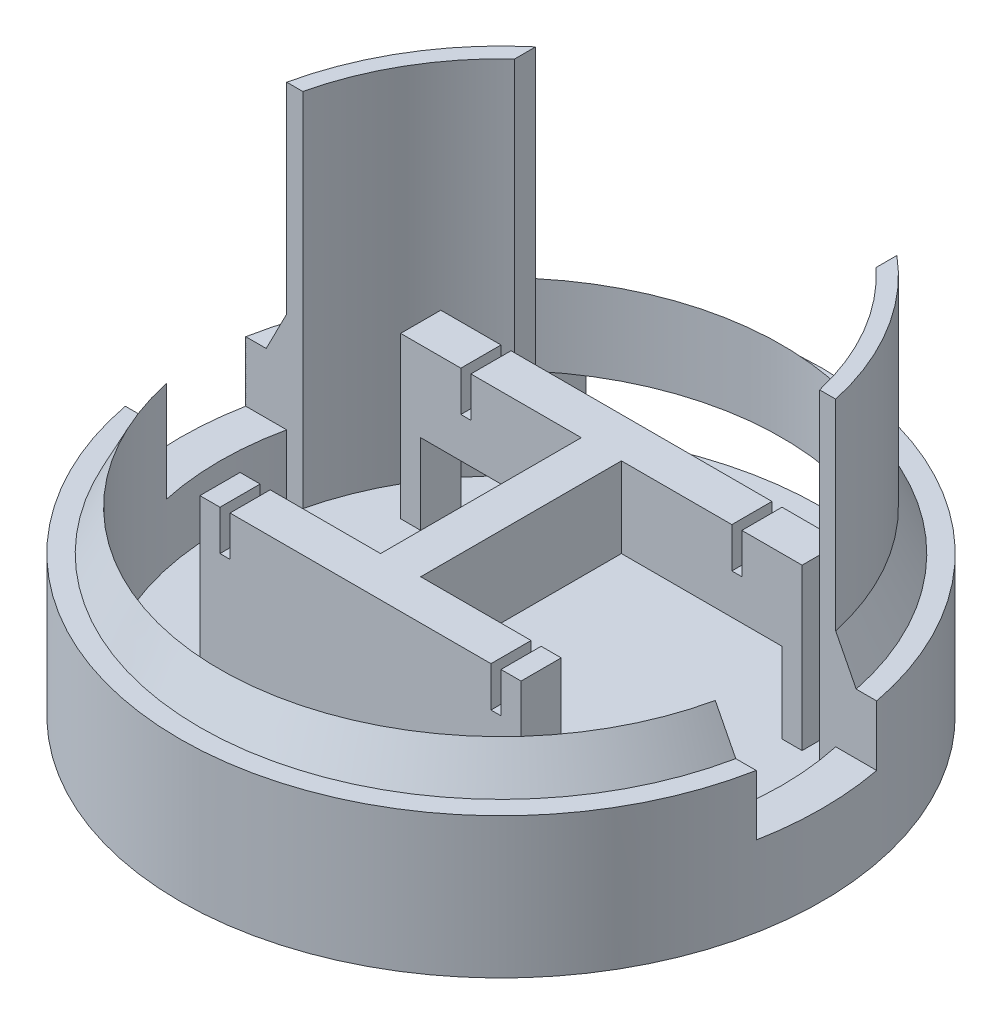
SolidWorks part; units mm, degrees
ref_plane "Front Plane" through (0, 0, 0) normal (0, 0, 1) x (1, 0, 0)
ref_plane "Top Plane" through (0, 0, 0) normal (0, 1, 0) x (1, 0, 0)
ref_plane "Right Plane" through (0, 0, 0) normal (1, 0, 0) x (0, 0, -1)
sketch "Sketch1" plane through (0, 0, 0) normal (0, 1, 0) x (1, 0, 0)
  circle A0 centre (0, 0) radius 50.8
  dimension "D1" = 101.6
extrude "Boss-Extrude1" add sketch "Sketch1" against normal blind 3.175
sketch "Sketch2" plane through (0, 0, 0) normal (0, 1, 0) x (1, 0, 0)
  circle A0 centre (0, 0) radius 50.8
  circle A1 centre (0, 0) radius 44.45
  circle A2 centre (0, 0) radius 50.8 construction
  dimension "D1" = 88.9
extrude "Boss-Extrude2" add sketch "Sketch2" along normal blind 19.05
sketch "Sketch3" plane through (0, 0, 0) normal (0, 0, 1) x (1, 0, 0)
  line L0 (44.45, 19.05) -> (50.8, 19.05) construction
  line L1 (50.8, 19.05) -> (-50.8, 19.05) construction
  line L2 (44.45, 19.05) -> (44.45, 25.4)
  line L9 (44.45, 25.4) -> (47.625, 19.05)
  line L10 (47.625, 19.05) -> (44.45, 19.05)
  point P4 (0, 0)
  dimension "D1" = 6.35
sketch "Sketch4" plane through (0, 0, 0) normal (1, 0, 0) x (0, 0, -1)
  line L0 (0, 6.35) -> (0, -6.35) construction
  point P3 (0, 0)
  dimension "D1" = 12.7
revolve "Revolve3" add sketch "Sketch3" angle 360 about L0
sketch "Sketch5" plane through (0, 0, 0) normal (0, 1, 0) x (1, 0, 0)
  line L1 (25.4, -22.225) -> (-25.4, -22.225)
  line L2 (25.4, -22.225) -> (25.4, -15.875)
  line L3 (25.4, -15.875) -> (-25.4, -15.875)
  line L4 (-25.4, -22.225) -> (-25.4, -15.875)
  line L5 (25.4, -22.225) -> (-25.4, -15.875) construction
  line L6 (25.4, -15.875) -> (-25.4, -22.225) construction
  point P0 (0, -19.05)
  point P5 (0, 0)
  dimension "D1" = 50.8
  dimension "D2" = 15.875
  dimension "D3" = 6.35
extrude "Boss-Extrude3" add sketch "Sketch5" along normal blind 25.4
sketch "Sketch6" plane through (0, 25.4, 0) normal (0, 1, 0) x (1, 0, 0)
  line L0 (25.4, -15.875) -> (-25.4, -15.875) construction
  line L1 (-22.225, -15.875) -> (-20.6375, -15.875)
  line L2 (-22.225, -15.875) -> (-22.225, -22.225)
  line L3 (-22.225, -22.225) -> (-20.6375, -22.225)
  line L4 (-20.6375, -15.875) -> (-20.6375, -22.225)
  line L5 (-25.4, -22.225) -> (25.4, -22.225) construction
  line L6 (-25.4, -15.875) -> (-25.4, -22.225) construction
  line L7 (20.6375, -15.875) -> (22.225, -15.875)
  line L8 (20.6375, -15.875) -> (20.6375, -22.225)
  line L9 (20.6375, -22.225) -> (22.225, -22.225)
  line L10 (22.225, -15.875) -> (22.225, -22.225)
  line L11 (25.4, -22.225) -> (25.4, -15.875) construction
  dimension "D1" = 3.175
  dimension "D2" = 3.175
  dimension "D3" = 1.5875
  dimension "D4" = 1.5875
extrude "Cut-Extrude1" cut sketch "Sketch6" against normal blind 6.35
sketch "Sketch7" plane through (0, 0, 0) normal (1, 0, 0) x (0, 0, -1)
  line L0 (-44.45, 25.4) -> (44.45, 25.4) construction
  line L1 (9.525, 25.4) -> (-9.525, 25.4)
  line L2 (9.525, 25.4) -> (9.525, 0)
  line L3 (9.525, 0) -> (-9.525, 0)
  line L4 (-9.525, 25.4) -> (-9.525, 0)
  dimension "D1" = 19.05
extrude "Cut-Extrude2" cut sketch "Sketch7" against normal through all both and the other way through all
sketch "Sketch8" plane through (0, 0, 0) normal (0, 0, 1) x (1, 0, 0)
  line L1 (28.575, 12.7) -> (-28.575, 12.7)
  line L2 (28.575, 12.7) -> (28.575, 0)
  line L3 (28.575, 0) -> (-28.575, 0)
  line L4 (-28.575, 12.7) -> (-28.575, 0)
  line L5 (28.575, 12.7) -> (-28.575, 0) construction
  line L6 (28.575, 0) -> (-28.575, 12.7) construction
  point P0 (0, 6.35)
  dimension "D1" = 57.15
  dimension "D2" = 12.7
extrude "Cut-Extrude3" cut sketch "Sketch8" against normal through all
sketch "Sketch9" plane through (0, 0, 0) normal (0, 1, 0) x (1, 0, 0)
  line L0 (-28.575, 34.0481) -> (-28.575, 30.7435)
  line L1 (-43.4175, 9.525) -> (-40.8775, 9.525)
  line L2 (28.575, 34.0481) -> (28.575, 30.7435)
  line L3 (43.4175, 9.525) -> (40.8775, 9.525)
  arc A0 (28.575, 34.0481) -> (43.4175, 9.525) centre (0, 0) cw
  arc A1 (43.4175, 9.525) -> (28.575, 34.0481) centre (0, 0) ccw construction
  arc A2 (-43.4175, 9.525) -> (-28.575, 34.0481) centre (0, 0) cw
  arc A3 (43.4175, 9.525) -> (-43.4175, 9.525) centre (0, 0) ccw construction
  arc A4 (-28.575, 34.0481) -> (-43.4175, 9.525) centre (0, 0) ccw construction
  arc A5 (-40.8775, 9.525) -> (-28.575, 30.7435) centre (0, 0) cw
  arc A6 (28.575, 30.7435) -> (40.8775, 9.525) centre (0, 0) cw
  point P24 (0, 0)
  dimension "D1" = 2.54
  dimension "D2" = 2.54
extrude "Boss-Extrude4" add sketch "Sketch9" along normal blind 57.15
sketch "Sketch10" plane through (0, 0, 15.875) normal (0, 0, -1) x (-1, 0, 0)
  line L1 (-3.175, 12.7) -> (3.175, 12.7)
  line L2 (-3.175, 12.7) -> (-3.175, 9.525)
  line L3 (-3.175, 9.525) -> (3.175, 9.525)
  line L4 (3.175, 12.7) -> (3.175, 9.525)
  line L6 (-25.4, 0) -> (25.4, 0) construction
  line L10 (0, 9.525) -> (0, 0) construction
  dimension "D1" = 3.175
  dimension "D2" = 9.525
  dimension "D3" = 6.35
extrude "Boss-Extrude5" add sketch "Sketch10" along normal blind 3.175
sketch "Sketch11" plane through (0, 0, 0) normal (0, 1, 0) x (1, 0, 0)
  line L1 (-31.75, 22.225) -> (-28.575, 22.225)
  line L2 (-31.75, 22.225) -> (-31.75, 15.875)
  line L3 (-31.75, 15.875) -> (-28.575, 15.875)
  line L4 (-28.575, 22.225) -> (-28.575, 15.875)
  line L5 (-31.75, 22.225) -> (-28.575, 15.875) construction
  line L6 (-31.75, 15.875) -> (-28.575, 22.225) construction
  line L7 (28.575, 22.225) -> (31.75, 22.225)
  line L8 (28.575, 22.225) -> (28.575, 15.875)
  line L9 (28.575, 15.875) -> (31.75, 15.875)
  line L10 (31.75, 22.225) -> (31.75, 15.875)
  line L11 (28.575, 22.225) -> (31.75, 15.875) construction
  line L12 (28.575, 15.875) -> (31.75, 22.225) construction
  line L15 (-28.575, 15.875) -> (28.575, 15.875) construction
  line L16 (0, 15.875) -> (0, -15.875) construction
  line L17 (25.4, -15.875) -> (-25.4, -15.875) construction
  point P0 (-30.1625, 19.05)
  point P5 (30.1625, 19.05)
  dimension "D1" = 3.175
  dimension "D2" = 3.175
  dimension "D3" = 57.15
  dimension "D4" = 6.35
extrude "Boss-Extrude6" add sketch "Sketch11" along normal blind 12.7
sketch "Sketch12" plane through (0, 12.7, 0) normal (0, 1, 0) x (1, 0, 0)
  line L1 (-31.75, 22.225) -> (31.75, 22.225)
  line L2 (-31.75, 22.225) -> (-31.75, 15.875)
  line L3 (-31.75, 15.875) -> (31.75, 15.875)
  line L4 (31.75, 22.225) -> (31.75, 15.875)
extrude "Boss-Extrude7" add sketch "Sketch12" along normal blind 12.7
mirror "Mirror1" about plane through (0, 0, 0) normal (0, 0, 1) of "Cut-Extrude1"
sketch "Sketch14" plane through (0, 0, -15.875) normal (0, 0, 1) x (1, 0, 0)
  line L0 (-20.6375, 25.4) -> (20.6375, 25.4) construction
  line L1 (-3.175, 25.4) -> (3.175, 25.4)
  line L2 (-3.175, 25.4) -> (-3.175, 12.7)
  line L3 (-3.175, 12.7) -> (3.175, 12.7)
  line L4 (3.175, 25.4) -> (3.175, 12.7)
  line L5 (-28.575, 12.7) -> (28.575, 12.7) construction
  point P8 (0, 12.7)
  dimension "D1" = 6.35
extrude "Boss-Extrude8" add sketch "Sketch14" along normal up to surface (31.75 mm away) up to face at (0, 19.05, 15.875)
sketch "Sketch15" plane through (0, 0, 0) normal (0, 1, 0) x (1, 0, 0)
  line L0 (-49.899, 9.525) -> (-40.8775, 9.525) construction
  line L1 (-49.899, 9.525) -> (-43.4175, 9.525)
  line L2 (43.4175, 9.525) -> (49.899, 9.525)
  line L3 (-49.899, -9.525) -> (-43.4175, -9.525)
  line L4 (43.4175, -9.525) -> (49.899, -9.525)
  arc A0 (-49.899, -9.525) -> (-49.899, 9.525) centre (0, 0) cw
  arc A1 (-43.4175, -9.525) -> (-43.4175, 9.525) centre (0, 0) cw
  arc A2 (43.4175, 9.525) -> (43.4175, -9.525) centre (0, 0) cw
  arc A3 (49.899, 9.525) -> (49.899, -9.525) centre (0, 0) cw
extrude "Boss-Extrude9" add sketch "Sketch15" along normal blind 9.525
